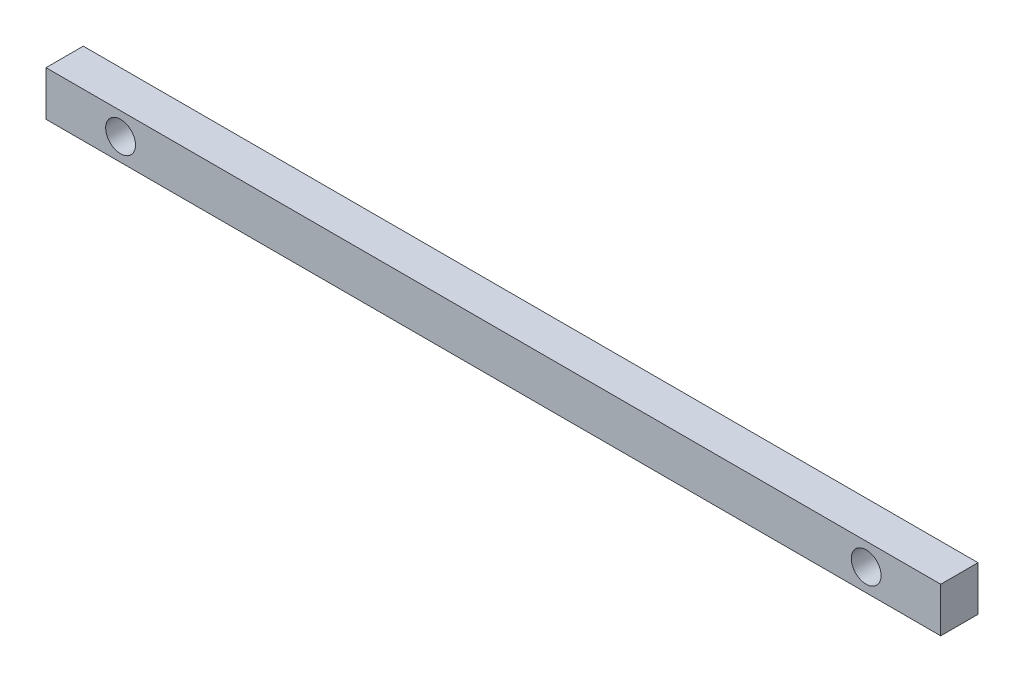
SolidWorks part; units mm, degrees
ref_plane "Front Plane" through (0, 0, 0) normal (0, 0, 1) x (1, 0, 0)
ref_plane "Top Plane" through (0, 0, 0) normal (0, 1, 0) x (1, 0, 0)
ref_plane "Right Plane" through (0, 0, 0) normal (1, 0, 0) x (0, 0, -1)
sketch "Sketch1" plane through (0, 0, 0) normal (0, 0, 1) x (1, 0, 0)
  line L1 (-60, -3) -> (60, -3)
  line L2 (-60, -3) -> (-60, 3)
  line L3 (-60, 3) -> (60, 3)
  line L4 (60, -3) -> (60, 3)
  line L7 (0, 3) -> (0, -3) construction
  circle A0 centre (-50, 0) radius 2
  circle A1 centre (50, 0) radius 2
  point P0 (0, 0)
extrude "Boss-Extrude1" add sketch "Sketch1" along normal blind 5
